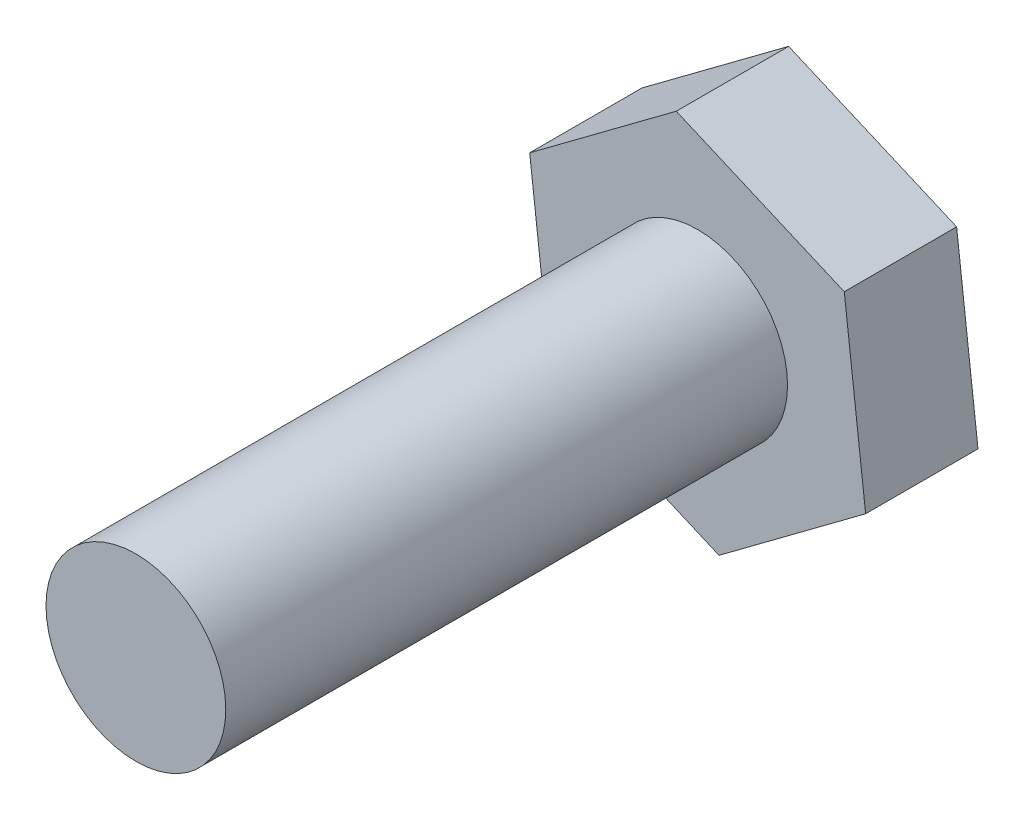
SolidWorks part; units mm, degrees
ref_plane "Front Plane" through (0, 0, 0) normal (0, 0, 1) x (1, 0, 0)
ref_plane "Top Plane" through (0, 0, 0) normal (0, 1, 0) x (1, 0, 0)
ref_plane "Right Plane" through (0, 0, 0) normal (1, 0, 0) x (0, 0, -1)
sketch "Sketch1" plane through (0, 0, 0) normal (0, 0, 1) x (1, 0, 0)
  line L1 (-0.9509, 8.0829) -> (-7.4755, 3.2179)
  line L2 (-7.4755, 3.2179) -> (-6.5245, -4.865)
  line L3 (-6.5245, -4.865) -> (0.9509, -8.0829)
  line L4 (0.9509, -8.0829) -> (7.4755, -3.2179)
  line L5 (7.4755, -3.2179) -> (6.5245, 4.865)
  line L6 (6.5245, 4.865) -> (-0.9509, 8.0829)
  circle A0 centre (0, 0) radius 7.0483 construction
  dimension "D1" = 14
extrude "Boss-Extrude1" add sketch "Sketch1" along normal blind 5
sketch "Sketch2" plane through (0, 0, 5) normal (0, 0, 1) x (1, 0, 0)
  circle A0 centre (0, 0) radius 4
  dimension "D1" = 8
extrude "Boss-Extrude2" add sketch "Sketch2" along normal blind 25
